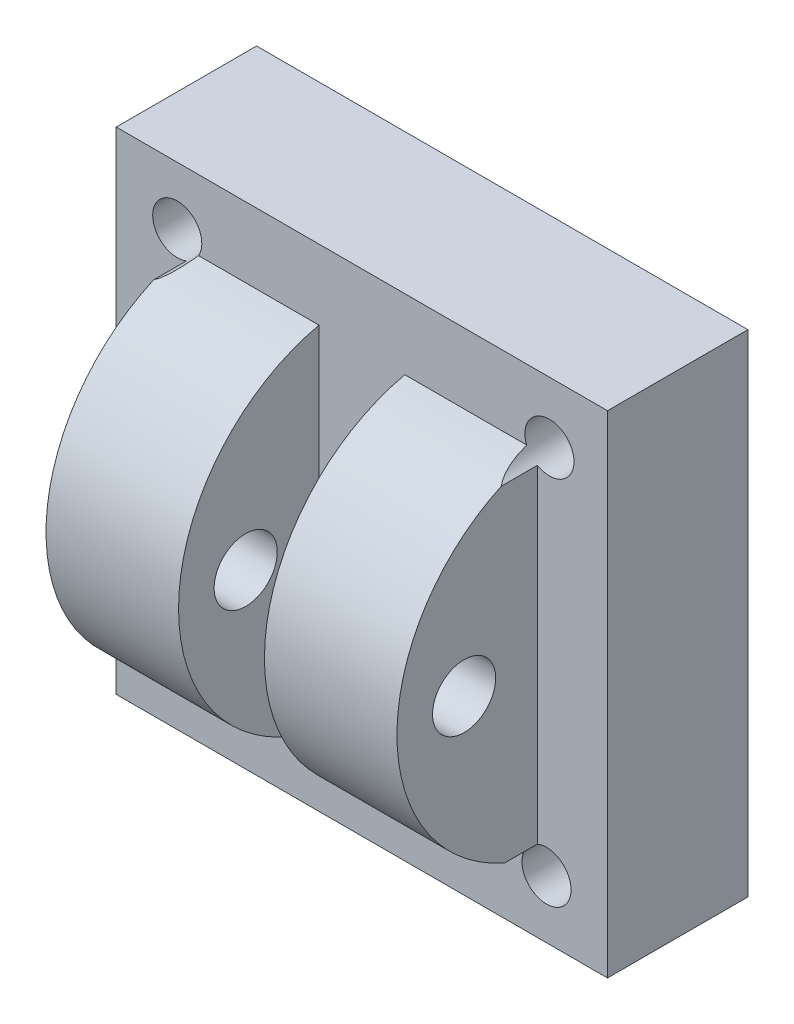
SolidWorks part; units mm, degrees
ref_plane "Front Plane" through (0, 0, 0) normal (0, 0, 1) x (1, 0, 0)
ref_plane "Top Plane" through (0, 0, 0) normal (0, 1, 0) x (1, 0, 0)
ref_plane "Right Plane" through (0, 0, 0) normal (1, 0, 0) x (0, 0, -1)
sketch "Sketch1" plane through (0, 0, 0) normal (0, 0, 1) x (1, 0, 0)
  line L1 (35, -35) -> (-35, -35)
  line L2 (35, -35) -> (35, 35)
  line L3 (35, 35) -> (-35, 35)
  line L4 (-35, -35) -> (-35, 35)
  line L5 (35, -35) -> (-35, 35) construction
  line L6 (35, 35) -> (-35, -35) construction
  point P0 (0, 0)
  dimension "D1" = 70
  dimension "D2" = 70
extrude "Boss-Extrude3" add sketch "Sketch1" along normal blind 20
sketch "Sketch5" plane through (0, 0, 20) normal (0, 0, 1) x (1, 0, 0)
  line L1 (-25, 25) -> (25, 25)
  line L2 (-25, 25) -> (-25, -25)
  line L3 (-25, -25) -> (25, -25)
  line L4 (25, 25) -> (25, -25)
  line L5 (-25, 25) -> (25, -25) construction
  line L6 (-25, -25) -> (25, 25) construction
  point P0 (0, 0)
  dimension "D1" = 50
  dimension "D2" = 50
extrude "Boss-Extrude4" add sketch "Sketch5" along normal blind 20
sketch "Sketch7" plane through (-25, 0, 0) normal (-1, 0, 0) x (0, 0, 1)
  line L0 (20, 25) -> (20, -25)
  arc A0 (20, 25) -> (20, -25) centre (14.375, 0) cw
extrude "Cut-Extrude5" cut sketch "Sketch7" against normal blind 80 flip side to cut
sketch "Sketch8" plane through (0, 0, 20) normal (0, 0, -1) x (-1, 0, 0)
  line L1 (-35, 35) -> (35, 35)
  line L2 (-35, 35) -> (-35, -35)
  line L3 (-35, -35) -> (35, -35)
  line L4 (35, 35) -> (35, -35)
  line L5 (-35, 35) -> (35, -35) construction
  line L6 (-35, -35) -> (35, 35) construction
  point P0 (0, 0)
  dimension "D1" = 70
  dimension "D2" = 70
extrude "Boss-Extrude5" add sketch "Sketch8" along normal blind 20
sketch "Sketch9" plane through (0, 0, 0) normal (0, 1, 0) x (1, 0, 0)
  line L0 (0, 0) -> (0, -47.0331) construction
  line L1 (-25, -30) -> (25, -30) construction
  line L2 (-25, -20) -> (-25, -40) construction
  line L3 (25, -40) -> (25, -20) construction
  line L4 (35, -20) -> (-35, -20) construction
  line L5 (-6.1193, -40) -> (6.1193, -40)
  line L6 (-6.1193, -40) -> (-6.1193, -20)
  line L7 (-6.1193, -20) -> (6.1193, -20)
  line L8 (6.1193, -40) -> (6.1193, -20)
  line L9 (-6.1193, -40) -> (6.1193, -20) construction
  line L10 (-6.1193, -20) -> (6.1193, -40) construction
  point P9 (0, -30)
  point P10 (0, -30)
extrude "Cut-Extrude6" cut sketch "Sketch9" against normal through all both and the other way through all
sketch "Sketch10" plane through (-25, 0, 0) normal (-1, 0, 0) x (0, 0, 1)
  line L0 (0, 0) -> (49.4401, 0) construction
  circle A0 centre (30.4341, 0) radius 4.5
  dimension "D1" = 9
extrude "Cut-Extrude7" cut sketch "Sketch10" against normal through all
sketch "Sketch11" plane through (0, 0, 0) normal (0, 0, -1) x (-1, 0, 0)
  line L1 (26.7252, -26.3062) -> (26.3062, 26.7252) construction
  line L2 (26.3062, 26.7252) -> (-26.7252, 26.3062) construction
  line L3 (-26.7252, 26.3062) -> (-26.3062, -26.7252) construction
  line L4 (-26.3062, -26.7252) -> (26.7252, -26.3062) construction
  circle A0 centre (0, 0) radius 25
  circle A1 centre (0, 0) radius 30
  circle A2 centre (0, 0) radius 37.5 construction
  circle A3 centre (0, 0) radius 26.5165 construction
  circle A4 centre (-26.7252, 26.3062) radius 3.5
  circle A5 centre (26.3062, 26.7252) radius 3.5
  circle A6 centre (26.7252, -26.3062) radius 3.5
  circle A7 centre (-26.3062, -26.7252) radius 3.5
  point P0 (0, 0)
  dimension "D1" = 50
  dimension "D2" = 60
  dimension "D3" = 75
  dimension "D4" = 7
  dimension "D5" = 7
  dimension "D6" = 7
  dimension "D7" = 7
extrude "Cut-Extrude10" cut sketch "Sketch11" against normal blind 5
sketch "Sketch14" plane through (0, 0, 0) normal (0, 0, -1) x (-1, 0, 0)
  circle A0 centre (-26.7252, 26.3062) radius 3.5
  circle A1 centre (26.3062, 26.7252) radius 3.5
  circle A2 centre (26.7252, -26.3062) radius 3.5
  circle A3 centre (-26.3062, -26.7252) radius 3.5
extrude "Cut-Extrude11" cut sketch "Sketch14" against normal blind 35
